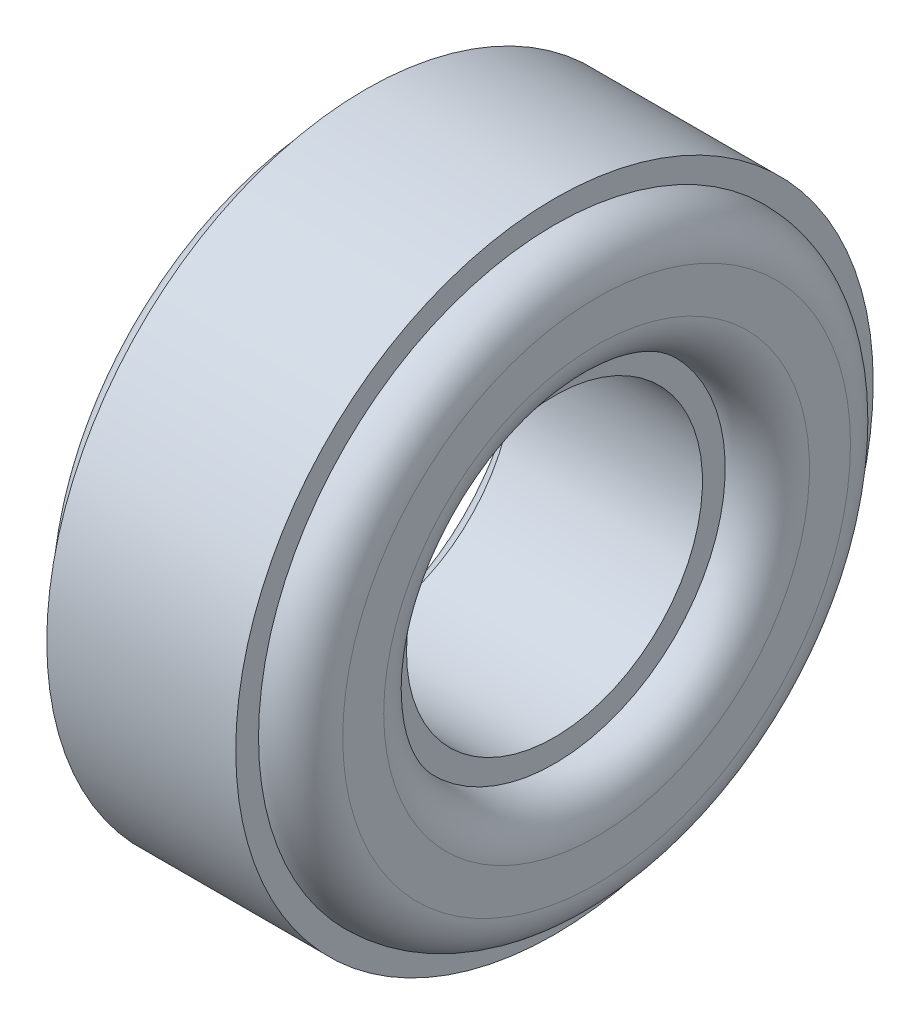
SolidWorks part; units mm, degrees
ref_plane "Front Plane" through (0, 0, 0) normal (0, 0, 1) x (1, 0, 0)
ref_plane "Top Plane" through (0, 0, 0) normal (0, 1, 0) x (1, 0, 0)
ref_plane "Right Plane" through (0, 0, 0) normal (1, 0, 0) x (0, 0, -1)
sketch "Sketch1" plane through (0, 0, 0) normal (0, 0, 1) x (1, 0, 0)
  line L0 (-8.833, 0) -> (12.3389, 0) construction
  line L1 (10.15, 9.35) -> (10.15, 11.15)
  line L2 (0, 14) -> (8.3, 14)
  line L3 (0, 14) -> (0, 13)
  line L4 (0, 6.5) -> (8.3, 6.5)
  line L5 (8.3, 14) -> (8.3, 13)
  line L6 (8.3, 7.5) -> (8.3, 6.5)
  line L7 (4.15, 6.5) -> (4.15, 14) construction
  line L8 (-1.85, 9.35) -> (-1.85, 11.15)
  line L9 (0, 7.5) -> (0, 6.5)
  arc A0 (8.3, 13) -> (10.15, 11.15) centre (8.3, 11.15) cw
  arc A1 (8.3, 7.5) -> (10.15, 9.35) centre (8.3, 9.35) ccw
  arc A2 (0, 7.5) -> (-1.85, 9.35) centre (0, 9.35) cw
  arc A3 (0, 13) -> (-1.85, 11.15) centre (0, 11.15) ccw
  point P21 (9.75, 8.91)
  dimension "D1" = 13
  dimension "D2" = 28
  dimension "D3" = 8.3
  dimension "D4" = 12
  dimension "D5" = 1
revolve "Revolve1" add sketch "Sketch1" angle 360 about L0
